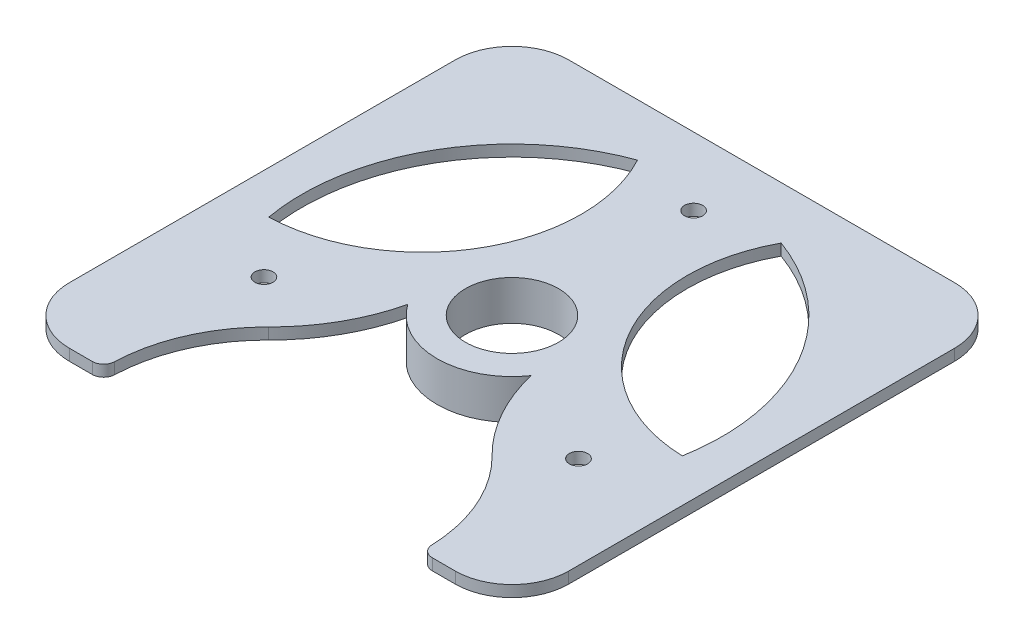
SolidWorks part; units mm, degrees
ref_plane "Front Plane" through (0, 0, 0) normal (0, 0, 1) x (1, 0, 0)
ref_plane "Top Plane" through (0, 0, 0) normal (0, 1, 0) x (1, 0, 0)
ref_plane "Right Plane" through (0, 0, 0) normal (1, 0, 0) x (0, 0, -1)
sketch "Sketch1" plane through (0, 0, 0) normal (0, 1, 0) x (1, 0, 0)
  line L0 (-44, 0) -> (-44, -44) construction
  line L1 (-44, -44) -> (44, -44) construction
  line L2 (44, -44) -> (44, 0) construction
  line L4 (-44, -44) -> (44, -44)
  line L5 (-44, -44) -> (-44, 44)
  line L6 (-44, 44) -> (44, 44)
  line L7 (44, -44) -> (44, 44)
  arc A0 (44, 0) -> (-44, 0) centre (0, 0) ccw construction
  dimension "D1" = 88
extrude "Boss-Extrude1" add sketch "Sketch1" along normal blind 2
fillet "Fillet1" radius 10 4 edges at (44, 1, 44) (-44, 1, 44) (44, 1, -44) (-44, 1, -44)
sketch "Sketch3" plane through (0, 2, 0) normal (0, 1, 0) x (1, 0, 0)
  circle A0 centre (0, 0) radius 37
  dimension "D1" = 74
extrude "Cut-Extrude2" cut sketch "Sketch3" against normal through all
sketch "Sketch5" plane through (0, 0, 0) normal (0, 1, 0) x (1, 0, 0)
  circle A0 centre (0, 0) radius 40.5
  circle A1 centre (0, 0) radius 10
  dimension "D1" = 20
extrude "Boss-Extrude2" add sketch "Sketch5" along normal up to surface (2 mm away) up to face at (0, 2, 37)
sketch "Sketch6" plane through (0, 2, 0) normal (0, 1, 0) x (1, 0, 0)
  line L0 (-12.6547, 34.7686) -> (0, 0) construction
  line L1 (0, 0) -> (12.6547, 34.7686) construction
  line L2 (0, -1000) -> (0, 49000) construction
  line L3 (-12.6547, 34.7686) -> (-9.9186, 27.2511)
  line L4 (9.9186, 27.2511) -> (12.6547, 34.7686)
  line L5 (36.4379, -6.425) -> (28.5594, -5.0358)
  line L6 (18.6408, -22.2153) -> (23.7831, -28.3436)
  line L7 (-23.7831, -28.3436) -> (-18.6408, -22.2153)
  line L8 (-28.5594, -5.0358) -> (-36.4379, -6.425)
  arc A0 (28.5594, -5.0358) -> (18.6408, -22.2153) centre (0, 0) cw
  arc A1 (-12.6547, 34.7686) -> (12.6547, 34.7686) centre (0, 0) cw
  arc A2 (-9.9186, 27.2511) -> (9.9186, 27.2511) centre (0, 0) cw
  circle A3 centre (0, 0) radius 37 construction
  arc A4 (36.4379, -6.425) -> (23.7831, -28.3436) centre (0, 0) cw
  arc A5 (-18.6408, -22.2153) -> (-28.5594, -5.0358) centre (0, 0) cw
  arc A6 (-23.7831, -28.3436) -> (-36.4379, -6.425) centre (0, 0) cw
  point P20 (0, 0)
  dimension "D3" = 8
  dimension "D4" = 74
  dimension "D1" = 20
  dimension "D2" = 20
  dimension "D5" = 3
sketch "Sketch16" plane through (0, 2, 0) normal (0, 1, 0) x (1, 0, 0)
  arc A0 (12.6547, 34.7686) -> (36.4379, -6.425) centre (37.307, 21.5392) ccw
  circle A1 centre (0, 0) radius 37 construction
  arc A2 (36.4379, -6.425) -> (12.6547, 34.7686) centre (0, 0) ccw
extrude "Cut-Extrude3" cut sketch "Sketch16" against normal through all
pattern_circular "CirPattern1" count 3 over 360 about axis through (0, 0, 0) along (0, 1, 0) of "Cut-Extrude3"
sketch "Sketch17" plane through (0, 2, 0) normal (0, 1, 0) x (1, 0, 0)
  circle A0 centre (0, -43.0784) radius 27.9777
  arc A1 (23.7831, -28.3436) -> (-23.7831, -28.3436) centre (0, -43.0784) ccw construction
extrude "Cut-Extrude4" cut sketch "Sketch17" against normal through all
sketch "Sketch18" plane through (0, 2, 0) normal (0, 1, 0) x (1, 0, 0)
  arc A0 (-10, 0) -> (-19.678, -23.1905) centre (-42.6237, 0) cw
  arc A1 (10, 0) -> (19.678, -23.1905) centre (42.6237, 0) ccw
  arc A2 (27.9625, -44) -> (-27.9625, -44) centre (0, -43.0784) ccw construction
  circle A3 centre (0, 0) radius 10 construction
  arc A4 (-10, 0) -> (10, 0) centre (0, 0) ccw
  arc A5 (19.678, -23.1905) -> (-19.678, -23.1905) centre (0, -43.0784) ccw
extrude "Cut-Extrude5" cut sketch "Sketch18" against normal through all
fillet "Fillet2" radius 2 2 edges at (27.9625, 1, 44) (-27.9625, 1, 44)
sketch "Sketch19" plane through (0, 0, 0) normal (0, -1, 0) x (1, 0, 0)
  circle A0 centre (0, 0) radius 8.2
  circle A1 centre (0, 0) radius 13.2
  dimension "D1" = 16.4
  dimension "D2" = 5
extrude "Boss-Extrude3" add sketch "Sketch19" along normal blind 5 and the other way up to surface (2 mm away) other way up to face at (-22.5603, 2, -13.0252)
sketch "Sketch20" plane through (0, 0, 0) normal (0, -1, 0) x (1, 0, 0)
  line L1 (0, -1000) -> (0, 49000) construction
  line L2 (0, -32) -> (0, 0) construction
  circle A0 centre (0, -32) radius 1.6
  dimension "D1" = 3.2
  dimension "D2" = 32
  dimension "D3" = 0
extrude "Cut-Extrude6" cut sketch "Sketch20" against normal through all
pattern_circular "CirPattern2" count 3 over 360 about axis through (0, 0, 0) along (0, 1, 0) of "Cut-Extrude6"
